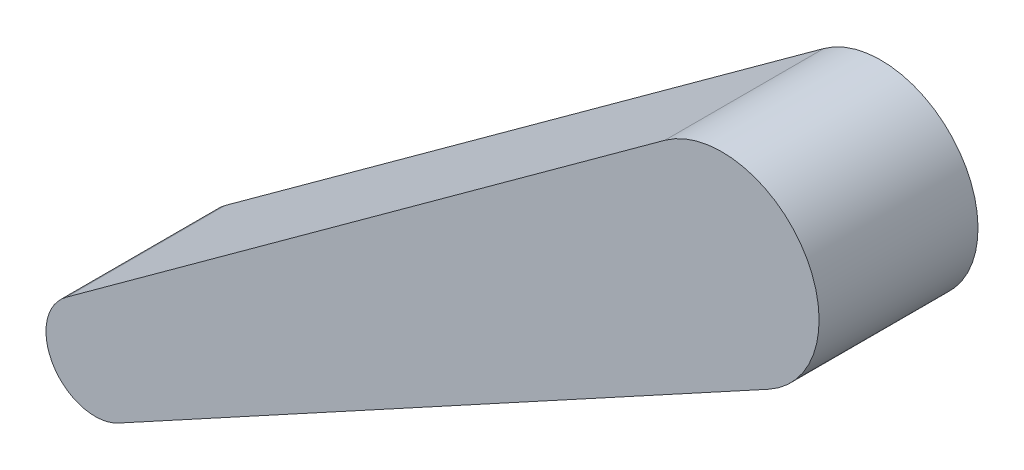
SolidWorks part; units mm, degrees
ref_plane "Front" through (0, 0, 0) normal (0, 0, 1) x (1, 0, 0)
ref_plane "Top" through (0, 0, 0) normal (0, 1, 0) x (1, 0, 0)
ref_plane "Right" through (0, 0, 0) normal (1, 0, 0) x (0, 0, -1)
sketch "Sketch1" plane through (0, 0, 0) normal (0, 0, 1) x (1, 0, 0)
  line L0 (-1507.5901, 476.3053) -> (-1958.4278, 191.2422) construction
  line L1 (-1507.5901, 476.3053) -> (-1958.4278, 191.2422)
  line L2 (-1548.6649, 532.8021) -> (-1979.1892, 219.7987)
  line L3 (-1474.1622, 414.9734) -> (-1941.5315, 160.2417)
  arc A0 (-1548.6649, 532.8021) -> (-1474.1622, 414.9734) centre (-1507.5901, 476.3053) cw
  arc A2 (-1475.2592, 538.2224) -> (-1543.6427, 416.4786) centre (-1507.5901, 476.3053) ccw construction
  arc A3 (-1941.5315, 160.2417) -> (-1979.1892, 219.7987) centre (-1958.4278, 191.2422) cw
  dimension "D1" = 35.306
extrude "Boss-Extrude1" add sketch "Sketch1" against normal blind 114.3
equation "\"mass\"= \"human weight@FS2-FR-HA-A-0001-V1, HUMAN ANALOG.Assembly\" * \"lower leg percent@FS2-FR-HA-A-0001-V1, HUMAN ANALOG.Assembly\""
